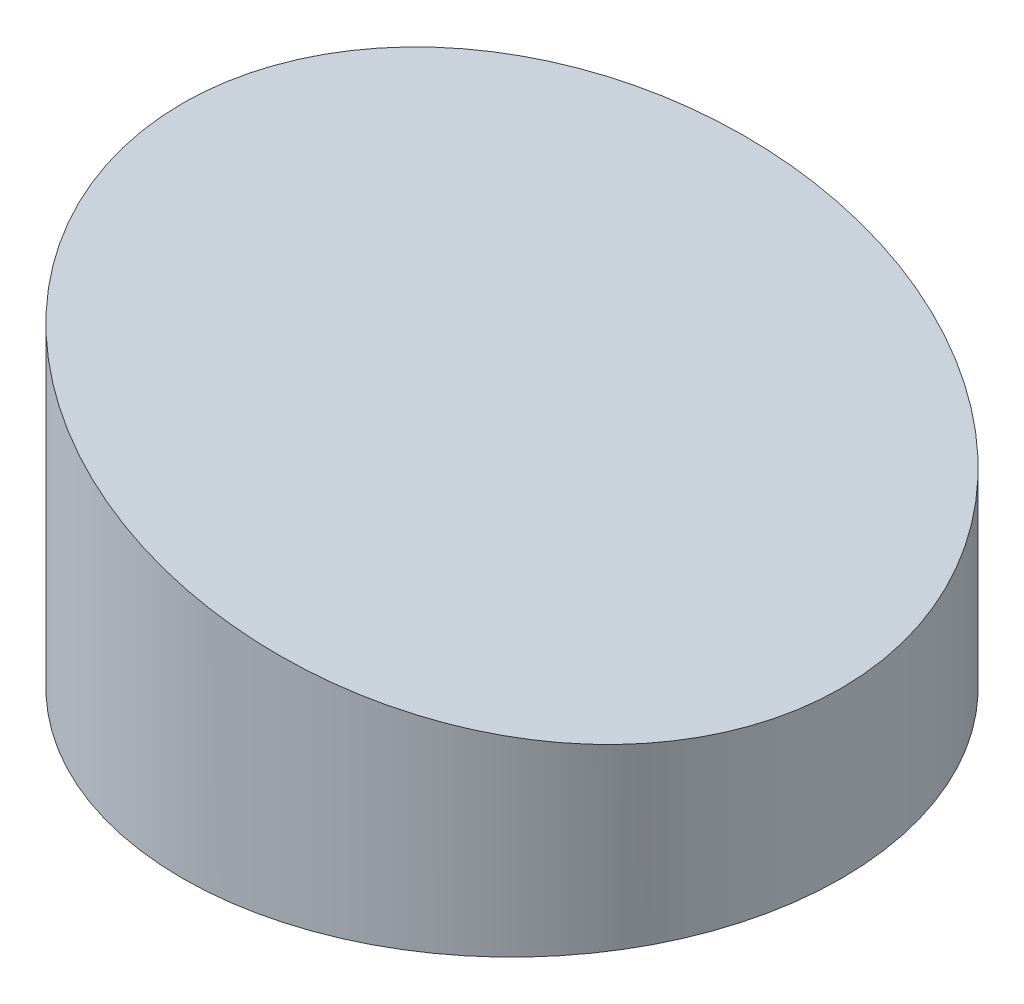
SolidWorks part; units mm, degrees
material "6061-T4 (SS)"
ref_plane "Front Plane" through (0, 0, 0) normal (0, 0, 1) x (1, 0, 0)
ref_plane "Top Plane" through (0, 0, 0) normal (0, 1, 0) x (1, 0, 0)
ref_plane "Right Plane" through (0, 0, 0) normal (1, 0, 0) x (0, 0, -1)
sketch "Sketch1" plane through (0, 0, 0) normal (0, 1, 0) x (1, 0, 0)
  circle A0 centre (0, 0) radius 12.7
  dimension "D1" = 25.4
extrude "Boss-Extrude1" add sketch "Sketch1" along normal blind 13.16
sketch "Sketch2" plane through (0, 0, 0) normal (0, 0, 1) x (1, 0, 0)
  line L0 (-12.7, 13.16) -> (12.7, 6.35)
  line L1 (12.7, 0) -> (12.7, 13.16) construction
  dimension "D1" = 6.35
extrude "Cut-Extrude4" cut sketch "Sketch2" against normal through all and the other way through all contours L0
sketch "Sketch4" plane through (0, 0, 0) normal (0, 1, 0) x (1, 0, 0)
  line L0 (-12.7, 0) -> (12.7, 0)
  circle A1 centre (0, 0) radius 12.7 construction
  circle A2 centre (-9.525, 0) radius 1.595
  circle A3 centre (0, 0) radius 9.525
  circle A4 centre (0.005, 0) radius 1.595
  circle A5 centre (9.535, 0) radius 1.595
  circle A7 centre (4.7625, 8.2489) radius 1.595
  circle A8 centre (4.7625, -8.2489) radius 1.595
  point P2 (9.4877, 0)
  point P8 (-9.525, 0)
  point P21 (0, 0)
  dimension "D1" = 19.05
  dimension "D2" = 3.19
  dimension "D3" = 3
  dimension "D4" = 3
extrude "Cut-Extrude9" cut sketch "Sketch4" along normal blind 4.32 contours A8 | A5 | A7 | A4 | A2
sketch "Sketch5" plane through (0, 0, 0) normal (0, -1, 0) x (-1, 0, 0)
  point P0 (-0.005, 0)
